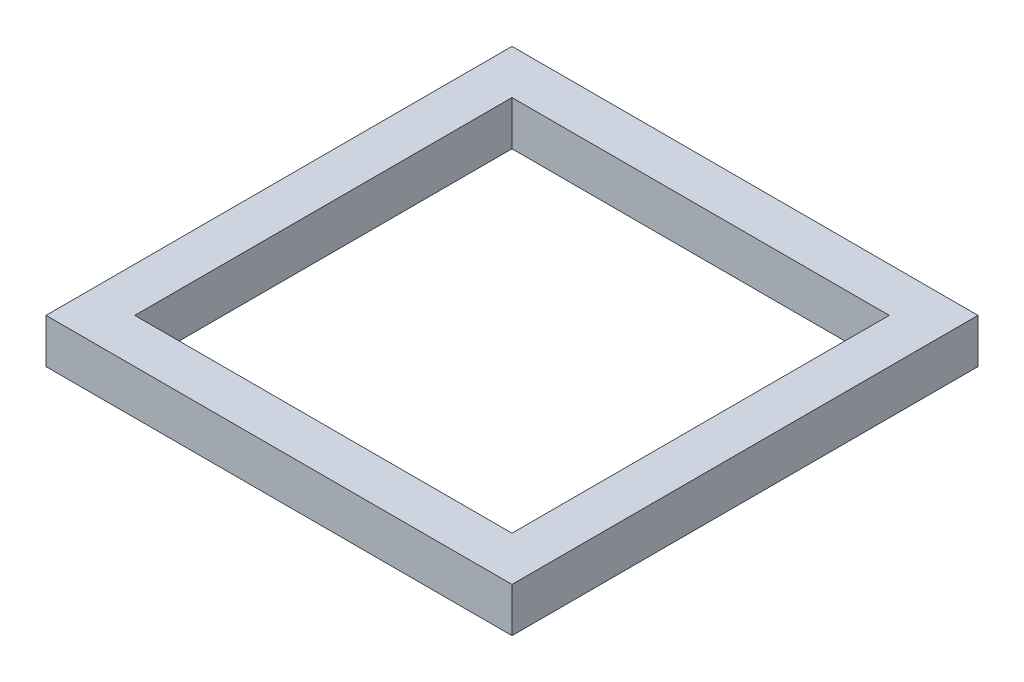
SolidWorks part; units mm, degrees
ref_plane "Front Plane" through (0, 0, 0) normal (0, 0, 1) x (1, 0, 0)
ref_plane "Top Plane" through (0, 0, 0) normal (0, 1, 0) x (1, 0, 0)
ref_plane "Right Plane" through (0, 0, 0) normal (1, 0, 0) x (0, 0, -1)
sketch "Sketch1" plane through (0, 0, 0) normal (0, 1, 0) x (1, 0, 0)
  line L1 (0, 0) -> (10.5, 0)
  line L2 (0, 0) -> (0, 10.5)
  line L3 (0, 10.5) -> (10.5, 10.5)
  line L4 (10.5, 0) -> (10.5, 10.5)
  dimension "D1" = 10.5
  dimension "D2" = 10.5
extrude "Boss-Extrude1" add sketch "Sketch1" along normal blind 1
sketch "Sketch2" plane through (0, 1, 0) normal (0, 1, 0) x (1, 0, 0)
  line L0 (5.25, 10.5) -> (5.25, 0) construction
  line L1 (10.5, 10.5) -> (0, 10.5) construction
  line L2 (0, 0) -> (10.5, 0) construction
  line L3 (0, 5.25) -> (10.5, 5.25) construction
  line L4 (0, 10.5) -> (0, 0) construction
  line L5 (10.5, 0) -> (10.5, 10.5) construction
  line L7 (1, 9.5) -> (9.5, 9.5)
  line L8 (1, 9.5) -> (1, 1)
  line L9 (1, 1) -> (9.5, 1)
  line L10 (9.5, 9.5) -> (9.5, 1)
  line L11 (1, 9.5) -> (9.5, 1) construction
  line L12 (1, 1) -> (9.5, 9.5) construction
  point P12 (5.25, 5.25)
  dimension "D1" = 1
extrude "Cut-Extrude1" cut sketch "Sketch2" against normal through all
